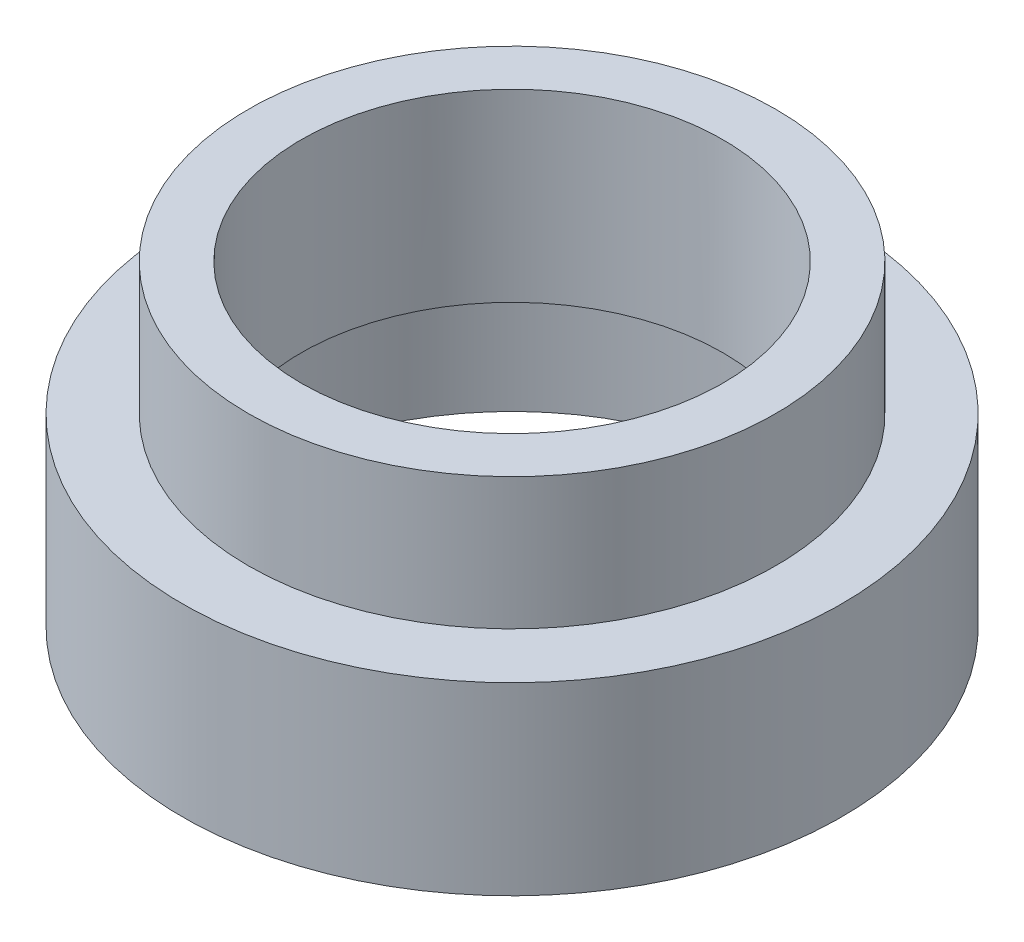
SolidWorks part; units mm, degrees
ref_plane "Front" through (0, 0, 0) normal (0, 0, 1) x (1, 0, 0)
ref_plane "Top" through (0, 0, 0) normal (0, 1, 0) x (1, 0, 0)
ref_plane "Right" through (0, 0, 0) normal (1, 0, 0) x (0, 0, -1)
sketch "Sketch1" plane through (0, 0, 0) normal (0, 1, 0) x (1, 0, 0)
  circle A0 centre (0, 0) radius 5
extrude "Boss-Extrude1" add sketch "Sketch1" along normal blind 2.5
sketch "Sketch2" plane through (0, 0, 0) normal (0, -1, 0) x (1, 0, 0)
  circle A0 centre (0, 0) radius 6.25
extrude "Boss-Extrude2" add sketch "Sketch2" along normal blind 3.5
sketch "Sketch3" plane through (0, 2.5, 0) normal (0, 1, 0) x (1, 0, 0)
  circle A0 centre (0, 0) radius 4
extrude "Cut-Extrude1" cut sketch "Sketch3" against normal blind 7.5
sketch "Sketch4" plane through (0, -3.5, 0) normal (0, -1, 0) x (1, 0, 0)
  circle A0 centre (0, 0) radius 5
extrude "Cut-Extrude2" cut sketch "Sketch4" against normal blind 2.5
